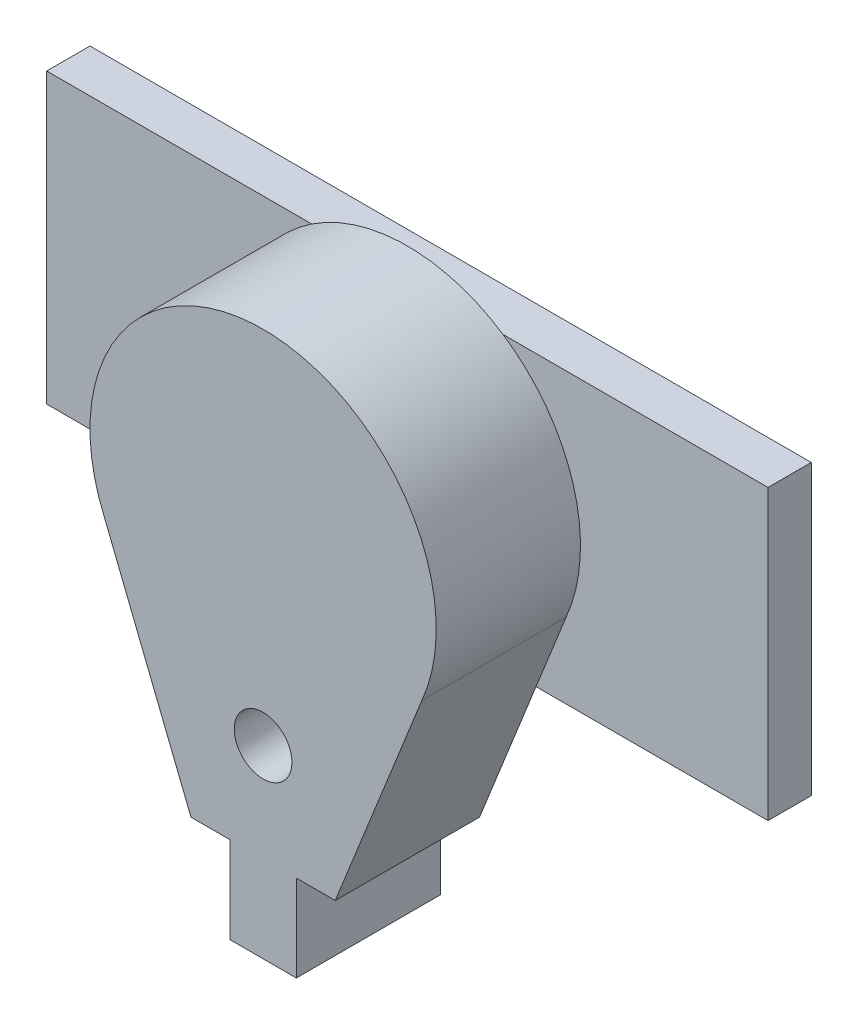
SolidWorks part; units mm, degrees
ref_plane "Plan de face" through (0, 0, 0) normal (0, 0, 1) x (1, 0, 0)
ref_plane "Plan de dessus" through (0, 0, 0) normal (0, 1, 0) x (1, 0, 0)
ref_plane "Plan de droite" through (0, 0, 0) normal (1, 0, 0) x (0, 0, -1)
sketch "Esquisse1" plane through (0, 0, 0) normal (0, 0, 1) x (1, 0, 0)
  line L0 (-11, -4.7958) -> (-5, -19.7958)
  line L1 (0, -55) -> (0, 55) construction
  line L2 (11, -4.7958) -> (5, -19.7958)
  line L3 (5, -19.7958) -> (-5, -19.7958)
  arc A0 (-11, -4.7958) -> (11, -4.7958) centre (0, 0) cw
  dimension "D4" = 12
  dimension "D1" = 22
  dimension "D2" = 10
  dimension "D3" = 15
extrude "Boss.-Extru.1" add sketch "Esquisse1" along normal blind 10
sketch "Esquisse2" plane through (0, 0, 0) normal (0, 0, -1) x (-1, 0, 0)
  circle A0 centre (0, -13) radius 2
  dimension "D1" = 4
  dimension "D2" = 13
extrude "Enlèv. mat.-Extru.1" cut sketch "Esquisse2" against normal blind 10
sketch "Esquisse4" plane through (0, -19.7958, 0) normal (0, -1, 0) x (-1, 0, 0)
  line L0 (-2.3053, -10) -> (2.3053, -10)
  line L1 (5, -10) -> (-5, -10) construction
  line L2 (2.3053, -10) -> (2.3053, 0)
  line L3 (5, 0) -> (-5, 0) construction
  line L4 (-2.3053, -10) -> (-2.3053, 0)
  line L5 (-2.3053, 0) -> (2.3053, 0)
  point P5 (0, -10)
extrude "Boss.-Extru.3" add sketch "Esquisse4" along normal blind 6
sketch "Esquisse3" plane through (0, 0, 0) normal (0, 0, -1) x (-1, 0, 0)
  line L0 (25, -10) -> (-25, -10)
  line L1 (25, -10) -> (25, 10)
  line L2 (-25, -10) -> (-25, 10)
  line L3 (25, 10) -> (-25, 10)
  line L4 (25, -10) -> (-25, 10) construction
  line L5 (-25, -10) -> (25, 10) construction
  point P1 (0, 0)
  dimension "D1" = 20
  dimension "D2" = 50
extrude "Boss.-Extru.2" add sketch "Esquisse3" along normal blind 3
